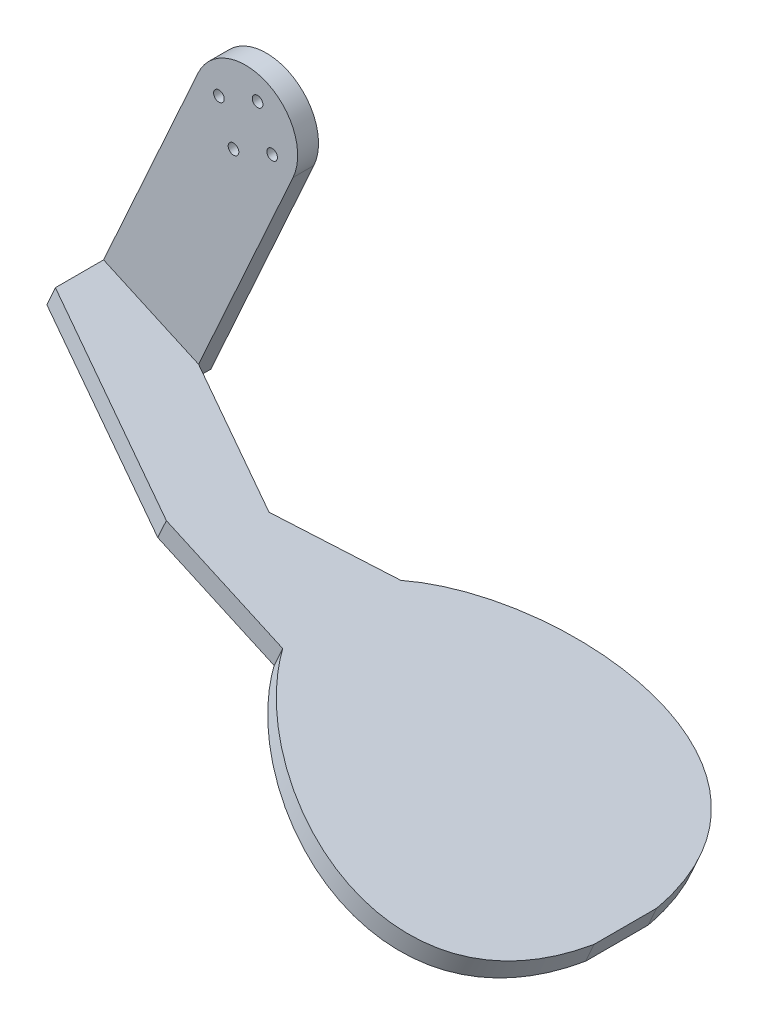
SolidWorks part; units mm, degrees
ref_plane "Front Plane" through (0, 0, 0) normal (0, 0, 1) x (1, 0, 0)
ref_plane "Top Plane" through (0, 0, 0) normal (0, 1, 0) x (1, 0, 0)
ref_plane "Right Plane" through (0, 0, 0) normal (1, 0, 0) x (0, 0, -1)
sketch "Sketch2" plane through (0, 0, 0) normal (0, 0, 1) x (1, 0, 0)
  line L0 (4.1189, 9.1123) -> (-4.1189, -9.1123) construction
  line L1 (-36.5208, -53.18) -> (-9.7479, 6.0501) construction
  line L2 (9.1123, -4.1189) -> (-9.1123, 4.1189) construction
  circle A0 centre (0, 0) radius 10
  circle A1 centre (2.8832, 6.3786) radius 1.275
  circle A4 centre (6.3786, -2.8832) radius 1.275
  circle A5 centre (0, 0) radius 10 construction
  circle A6 centre (-2.8832, -6.3786) radius 1.275
  circle A7 centre (-6.3786, 2.8832) radius 1.275
  point P21 (0, 0)
  dimension "D1" = 2.55
  dimension "D2" = 2.55
  dimension "D3" = 7
  dimension "D4" = 7
extrude "Boss-Extrude1" add sketch "Sketch2" along normal blind 3
sketch "Sketch3" plane through (0, 0, 3) normal (0, 0, 1) x (1, 0, 0)
  line L0 (5.1486, 11.3904) -> (-5.1486, -11.3904) construction
  line L1 (11.3904, -5.1486) -> (-11.3904, 5.1486) construction
  line L3 (11.3904, -5.1486) -> (-13.323, -59.8226)
  line L4 (-11.3904, 5.1486) -> (-36.1039, -49.5254)
  line L5 (-13.323, -59.8226) -> (-36.1039, -49.5254)
  line L6 (-36.5208, -53.18) -> (-9.7479, 6.0501) construction
  arc A0 (11.3904, -5.1486) -> (-11.3904, 5.1486) centre (0, 0) ccw
  circle A1 centre (2.8832, 6.3786) radius 1.275
  circle A2 centre (6.3786, -2.8832) radius 1.275
  circle A3 centre (-2.8832, -6.3786) radius 1.275
  circle A4 centre (-6.3786, 2.8832) radius 1.275
  circle A5 centre (0, 0) radius 10 construction
  point P14 (0, 0)
  dimension "D1" = 2.55
  dimension "D2" = 2.55
  dimension "D5" = 25
  dimension "D3" = 7
  dimension "D4" = 7
  dimension "D6" = 60
extrude "Boss-Extrude2" add sketch "Sketch3" against normal blind 5
sketch "Sketch4" plane through (-24.7135, -54.674, 0) normal (-0.4119, -0.9112, 0) x (-0.9112, 0.4119, 0)
  line L2 (-64.738, -30.422) -> (-34.1151, -30.422)
  line L5 (12.5, -3) -> (-12.5, -3)
  line L9 (-64.738, -2.102) -> (-42.1016, -13.0783)
  line L10 (12.5, -3) -> (12.5, -14.5513)
  line L11 (7.4752, -16.262) -> (-142.2578, -16.262) construction
  line L12 (-139.3816, -8.762) -> (-139.3816, -23.762)
  line L13 (12.5, -14.5513) -> (-34.1151, -30.422)
  line L14 (-12.5, -3) -> (-42.1016, -13.0783)
  line L17 (12.5, 2) -> (12.5, -3) construction
  spline S0 degree 3 poles (-64.738, -2.102) (-81.7618, 22.4199) (-132.6192, 37.6495) (-139.3816, -8.762) knots 0 0 0 0 1 1 1 1
  spline S1 degree 3 poles (-64.738, -30.422) (-81.7618, -54.944) (-132.6192, -70.1735) (-139.3816, -23.762) knots 0 0 0 0 1 1 1 1
  point P8 (-79.378, 11.738)
  point P11 (-114.5582, 20.788)
  point P17 (-139.3816, -8.762)
  dimension "D1" = 18.9923
  dimension "D2" = 25.1572
  dimension "D3" = 31.2702
extrude "Boss-Extrude3" add sketch "Sketch4" against normal blind 5
